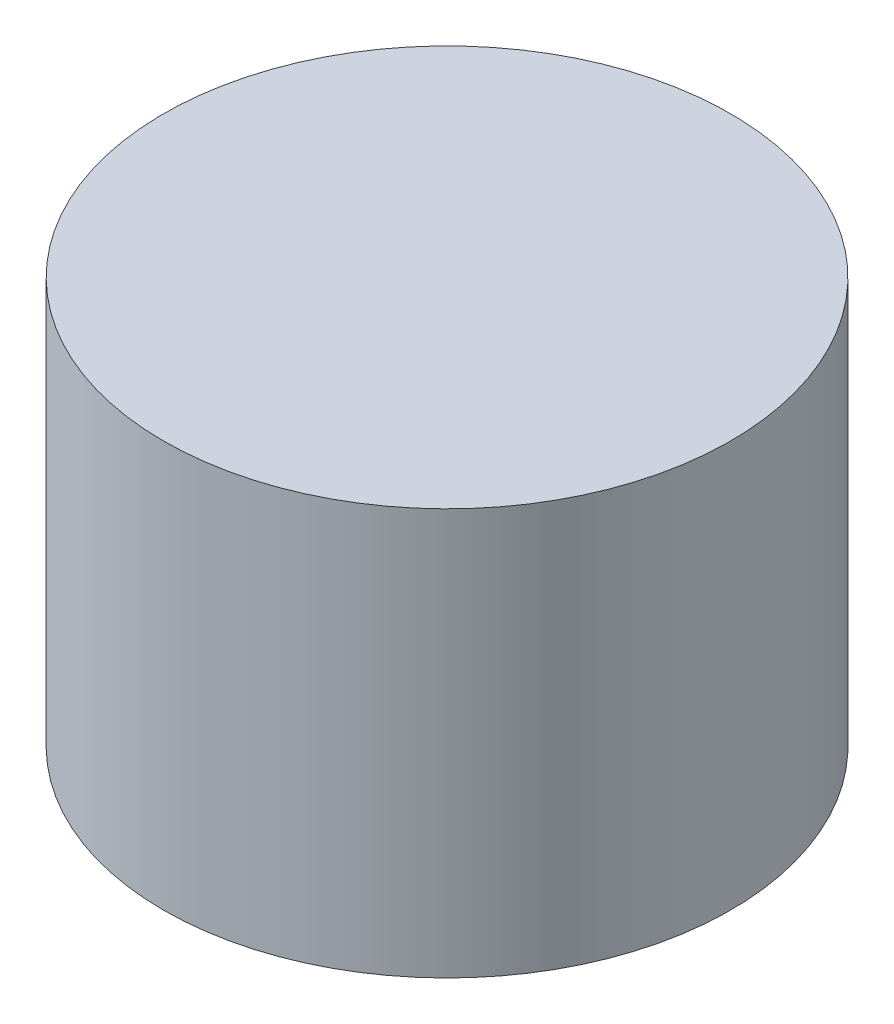
SolidWorks part; units mm, degrees
ref_plane "Front" through (0, 0, 0) normal (0, 0, 1) x (1, 0, 0)
ref_plane "Top" through (0, 0, 0) normal (0, 1, 0) x (1, 0, 0)
ref_plane "Right" through (0, 0, 0) normal (1, 0, 0) x (0, 0, -1)
sketch "Sketch1" plane through (0, 0, 0) normal (0, 1, 0) x (1, 0, 0)
  circle A0 centre (0, 0) radius 15
  dimension "D1" = 30
extrude "Boss-Extrude1" add sketch "Sketch1" along normal blind 21.5
